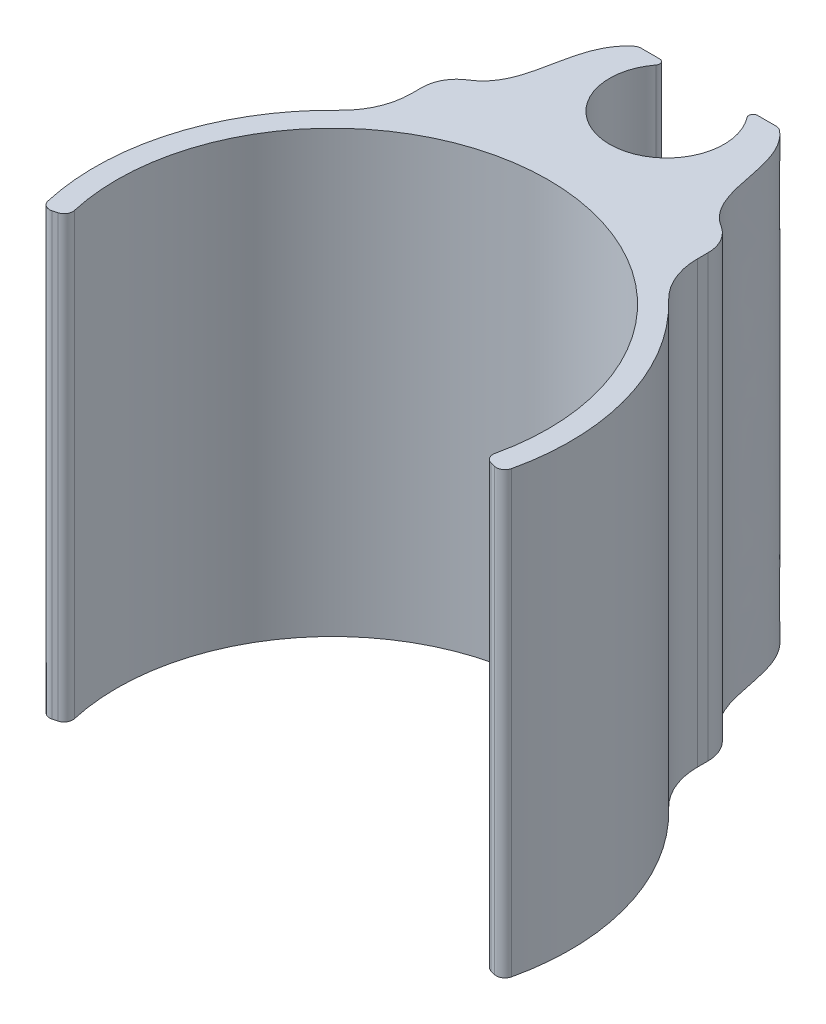
SolidWorks part; units mm, degrees
ref_plane "Front" through (0, 0, 0) normal (0, 0, 1) x (1, 0, 0)
ref_plane "Top" through (0, 0, 0) normal (0, 1, 0) x (1, 0, 0)
ref_plane "Right" through (0, 0, 0) normal (1, 0, 0) x (0, 0, -1)
sketch "Sketch1" plane through (0, 0, 0) normal (0, 1, 0) x (1, 0, 0)
  line L0 (-13.2486, -3.55) -> (13.2486, -3.55) construction
  line L1 (-13.2486, -3.55) -> (0, 0) construction
  line L2 (0, 0) -> (13.2486, -3.55) construction
  line L3 (-13.2486, -3.55) -> (-12.0219, -3.2213)
  line L4 (12.0219, -3.2213) -> (13.2486, -3.55)
  line L6 (0, 14.716) -> (0, 13.716) construction
  line L7 (-8.255, 14.716) -> (-8.255, 10.9537)
  line L8 (8.255, 14.716) -> (8.255, 10.9537)
  line L9 (-8.255, 14.716) -> (-8.255, 21.701)
  line L10 (-8.255, 21.701) -> (8.255, 21.701)
  line L11 (8.255, 21.701) -> (8.255, 14.716)
  arc A0 (13.2486, -3.55) -> (8.255, 10.9537) centre (0, 0) ccw
  arc A1 (-12.0219, -3.2213) -> (12.0219, -3.2213) centre (0, 0) cw
  arc A2 (-8.255, 10.9537) -> (-13.2486, -3.55) centre (0, 0) ccw
  point P10 (0, 21.701)
  dimension "D2" = 12.446
  dimension "D3" = 1.27
  dimension "D1" = 210
  dimension "D4" = 1
  dimension "D5" = 16.51
  dimension "D6" = 6.985
extrude "Boss-Extrude1" add sketch "Sketch1" along normal blind 25.4
sketch "Sketch2" plane through (0, 25.4, 0) normal (0, 1, 0) x (1, 0, 0)
  line L0 (-8.255, 21.701) -> (-8.255, 14.716)
  line L1 (-8.255, 21.701) -> (-8.255, 10.9537) construction
  line L2 (8.255, 21.701) -> (8.255, 14.716)
  line L3 (8.255, 10.9537) -> (8.255, 21.701) construction
  line L4 (-8.255, 21.701) -> (-4.0631, 21.701)
  line L5 (8.255, 21.701) -> (-8.255, 21.701) construction
  line L6 (8.255, 21.701) -> (4.0631, 21.701)
  line L7 (0, 13.716) -> (0, 19.2882) construction
  circle A0 centre (0, 19.2882) radius 3.302
  arc A3 (-8.255, 10.9537) -> (-13.2486, -3.55) centre (0, 0) ccw construction
  spline S0 degree 3 poles (-8.255, 14.716) (-4.7393, 15.6362) (-6.5192, 19.8931) (-4.0631, 21.701) knots 0 0 0 0 1 1 1 1
  spline S1 degree 3 poles (8.255, 14.716) (4.7393, 15.6362) (6.5192, 19.8931) (4.0631, 21.701) knots 0 0 0 0 1 1 1 1
  point P2 (0, 13.716)
  point P6 (0, 14.716)
  dimension "D2" = 6.604
  dimension "D1" = 1
  dimension "D3" = 4.5722
  dimension "D4" = 4.1919
  dimension "D5" = 1.9784
  dimension "D6" = 1.5465
  dimension "D7" = 1.2455
  dimension "D8" = 3.1902
extrude "Cut-Extrude1" cut sketch "Sketch2" against normal up to surface (25.4 mm away) up to face at (0, 0, -8.6201)
fillet "Fillet1" radius 0.508 2 edges at (-4.0631, 12.7, -21.701) (4.0631, 12.7, -21.701)
fillet "Fillet2" radius 0.254 2 edges at (-2.2542, 12.7, -21.701) (2.2542, 12.7, -21.701)
fillet "Fillet3" radius 2 2 edges at (-8.255, 12.7, -14.716) (8.255, 12.7, -14.716)
fillet "Fillet4" radius 4 2 edges at (-8.255, 12.7, -10.9537) (8.255, 12.7, -10.9537)
fillet "Fillet5" radius 0.5 4 edges at (13.2486, 12.7, 3.55) (12.0219, 12.7, 3.2213) (-12.0219, 12.7, 3.2213) (-13.2486, 12.7, 3.55)
